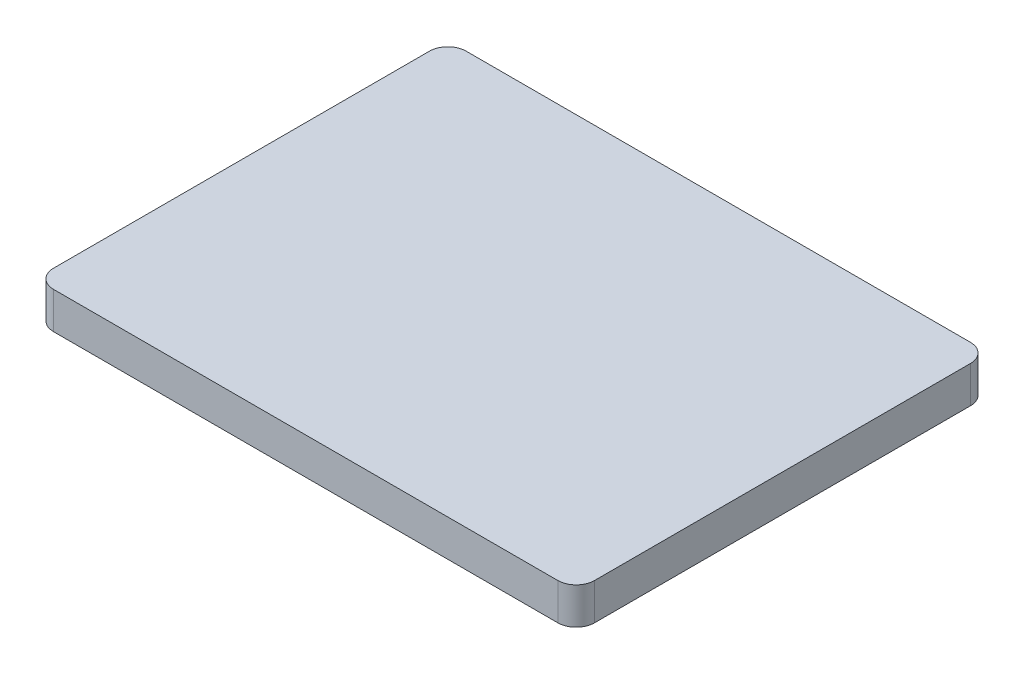
SolidWorks part; units mm, degrees
ref_plane "Front" through (0, 0, 0) normal (0, 0, 1) x (1, 0, 0)
ref_plane "Top" through (0, 0, 0) normal (0, 1, 0) x (1, 0, 0)
ref_plane "Right" through (0, 0, 0) normal (1, 0, 0) x (0, 0, -1)
sketch "草图2" plane through (0, 0, 0) normal (0, 1, 0) x (1, 0, 0)
  line L1 (-14.75, 11.25) -> (14.75, 11.25)
  line L2 (-14.75, 11.25) -> (-14.75, -11.25)
  line L3 (-14.75, -11.25) -> (14.75, -11.25)
  line L4 (14.75, 11.25) -> (14.75, -11.25)
  line L5 (-14.75, 11.25) -> (14.75, -11.25) construction
  line L6 (-14.75, -11.25) -> (14.75, 11.25) construction
  point P0 (0, 0)
  dimension "D1" = 29.5
  dimension "D2" = 22.5
extrude "layer" add sketch "草图2" along normal blind 2
fillet "圆角1" radius 1 4 edges at (14.75, 1, 11.25) (-14.75, 1, 11.25) (-14.75, 1, -11.25) (14.75, 1, -11.25)
